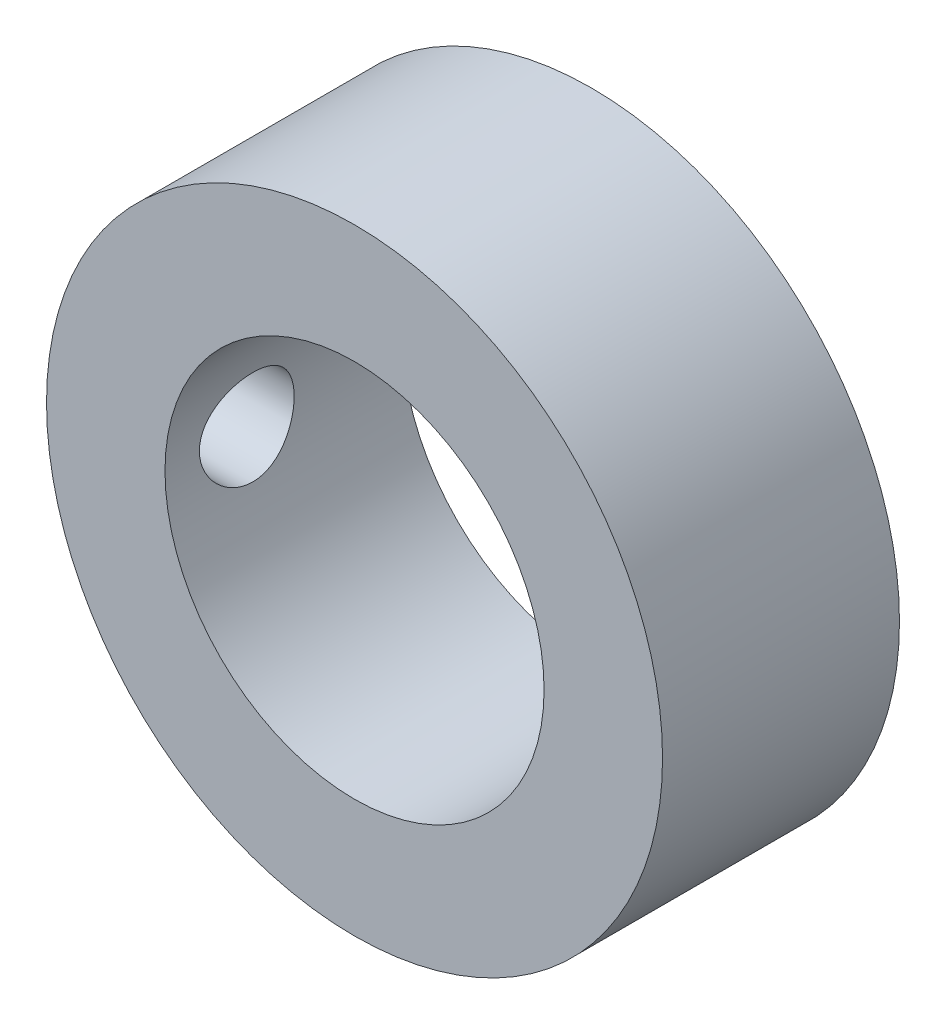
SolidWorks part; units mm, degrees
ref_plane "Plan de face" through (0, 0, 0) normal (0, 0, 1) x (1, 0, 0)
ref_plane "Plan de dessus" through (0, 0, 0) normal (0, 1, 0) x (1, 0, 0)
ref_plane "Plan de droite" through (0, 0, 0) normal (1, 0, 0) x (0, 0, -1)
sketch "Esquisse1" plane through (0, 0, 0) normal (0, 0, 1) x (1, 0, 0)
  circle A0 centre (0, 0) radius 6.5
  circle A1 centre (0, 0) radius 4
extrude "Extrusion1" add sketch "Esquisse1" along normal blind 5
sketch "Esquisse2" plane through (0, 0, 0) normal (1, 0, 0) x (0, 0, -1)
  line L0 (0.2255, 0) -> (-5, 0) construction
  line L1 (-2.3873, 0) -> (-2.3873, 2.1396) construction
  line L2 (-5, 6.5) -> (-5, -6.5) construction
  circle A0 centre (-3.2745, 0) radius 1
extrude "Extrusion2" cut sketch "Esquisse2" against normal through all
